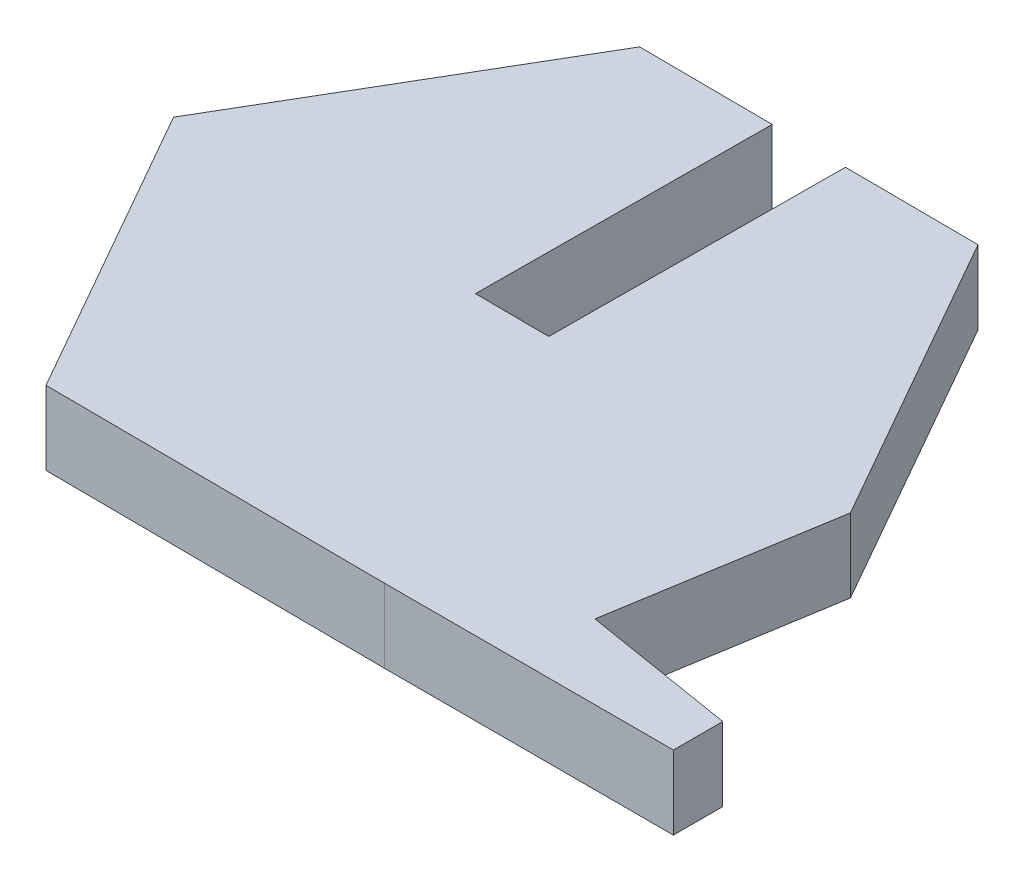
SolidWorks part; units mm, degrees
ref_plane "Front Plane" through (0, 0, 0) normal (0, 0, 1) x (1, 0, 0)
ref_plane "Top Plane" through (0, 0, 0) normal (0, 1, 0) x (1, 0, 0)
ref_plane "Right Plane" through (0, 0, 0) normal (1, 0, 0) x (0, 0, -1)
sketch "Sketch1" plane through (0, 0, 0) normal (0, 1, 0) x (1, 0, 0)
  line L0 (11.5468, -0.0722) -> (10.3299, -7.5164)
  line L2 (11.5468, -0.0722) -> (5.836, 9.9637)
  line L3 (5.836, 9.9637) -> (-5.7108, 10.0359)
  line L4 (-5.7108, 10.0359) -> (-11.5468, 0.0722)
  line L5 (-11.5468, 0.0722) -> (-5.836, -9.9637)
  line L6 (-5.836, -9.9637) -> (5.7108, -10.0359)
  line L7 (10.3299, -7.5164) -> (15.5082, -8.363)
  line L8 (15.5082, -8.363) -> (15.5082, -10.0359)
  line L9 (15.5082, -10.0359) -> (5.7108, -10.0359)
  line L11 (5.7108, -10.0359) -> (11.5468, -0.0722) [skipped]
  circle A0 centre (0, 0) radius 10 construction
  dimension "D1" = 20
extrude "Boss-Extrude1" add sketch "Sketch1" along normal blind 2.5
sketch "Sketch7" plane through (-0.0626, 0, 9.9998) normal (-0.0063, 0, 1) x (1, 0, 0.0063)
  line L0 (-5.7735, 0) -> (5.7735, 0) construction
  line L1 (-1.247, 0) -> (1.253, 0)
  line L2 (-1.247, 0) -> (-1.247, 2.5)
  line L3 (-1.247, 2.5) -> (1.253, 2.5)
  line L4 (1.253, 0) -> (1.253, 2.5)
  line L5 (-5.7735, 2.5) -> (5.7735, 2.5) construction
  line L6 (-11.547, 2.5) -> (-11.547, 0) construction
  dimension "D1" = 10.3
  dimension "D2" = 2.5
sketch "Sketch8" plane through (0.0626, 0, -9.9998) normal (0.0063, 0, -1) x (-1, 0, -0.0063)
  line L0 (-5.7735, 2.5) -> (5.7735, 2.5) construction
  line L1 (1.247, 2.5) -> (-1.253, 2.5)
  line L2 (1.247, 2.5) -> (1.247, 0)
  line L3 (1.247, 0) -> (-1.253, 0)
  line L4 (-1.253, 2.5) -> (-1.253, 0)
  line L5 (-5.7735, 0) -> (5.7735, 0) construction
  dimension "D1" = 2.5
  dimension "D2" = 10.3
extrude "Cut-Extrude1" cut sketch "Sketch8" against normal blind 10
